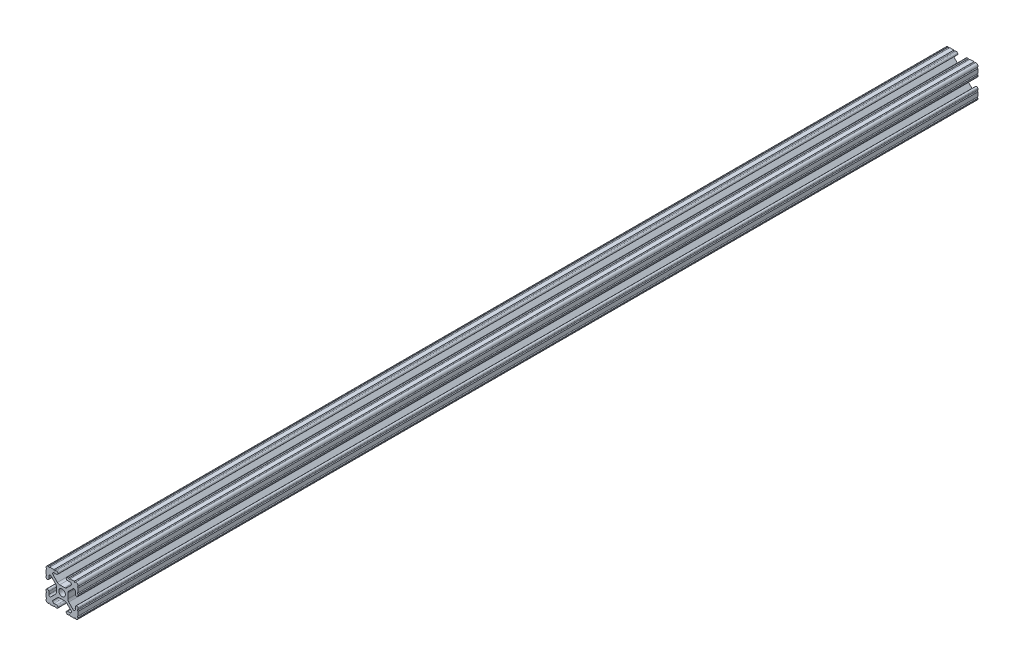
SolidWorks part; units mm, degrees
ref_plane "Front Plane" through (0, 0, 0) normal (0, 0, 1) x (1, 0, 0)
ref_plane "Top Plane" through (0, 0, 0) normal (0, 1, 0) x (1, 0, 0)
ref_plane "Right Plane" through (0, 0, 0) normal (1, 0, 0) x (0, 0, -1)
sketch "Sketch1" plane through (0, 0, 0) normal (0, 0, 1) x (1, 0, 0)
  line L0 (0, -12.7) -> (0, 12.7) construction
  line L1 (12.7, 0) -> (-12.7, 0) construction
  line L2 (3.2512, 12.7) -> (-3.2512, 12.7) construction
  line L3 (0, -4.5212) -> (0, 4.5212) construction
  line L4 (-3.2512, 12.7) -> (-3.2512, 10.4902) construction
  line L5 (12.7, -7.4168) -> (12.7, 7.4168) construction
  line L6 (0, -2.6035) -> (0, 2.6035) construction
  point P4 (0, 0)
  point P8 (0, 0)
  point P11 (0, 12.7)
  point P14 (0, 0)
  point P18 (12.7, 0)
  point P21 (0, 0)
sketch "Sketch2" plane through (0, 0, 0) normal (1, 0, 0) x (0, 0, -1)
  line L0 (-355.6, 0) -> (355.6, 0) construction
  point P4 (0, 0)
  dimension "Length" = 711.2
sketch "Sketch3" plane through (0, 0, 0) normal (0, 0, 1) x (1, 0, 0)
  line L1 (12.7, -12.7) -> (-12.7, -12.7)
  line L2 (12.7, -12.7) -> (12.7, 12.7)
  line L3 (12.7, 12.7) -> (-12.7, 12.7)
  line L4 (-12.7, -12.7) -> (-12.7, 12.7)
  line L5 (12.7, -12.7) -> (-12.7, 12.7) construction
  line L6 (12.7, 12.7) -> (-12.7, -12.7) construction
  point P0 (0, 0)
extrude "Boss-Extrude1" add sketch "Sketch3" along normal up to vertex (355.6 mm away) and the other way up to vertex (355.6 mm away) up to point (0, 0, 355.6) other way up to point (0, 0, -355.6)
sketch "Sketch4" plane through (0, 0, 355.6) normal (0, 0, 1) x (1, 0, 0)
  line L0 (-3.2512, 12.7) -> (-3.2512, 10.4902)
  line L1 (-3.2512, 10.4902) -> (-8.9276, 10.4902)
  line L2 (-8.9276, 10.4902) -> (-2.9586, 4.5212)
  line L3 (-2.9586, 4.5212) -> (2.9586, 4.5212)
  line L4 (0, -12.7) -> (0, 12.7) construction
  line L5 (12.7, 12.7) -> (-12.7, 12.7) construction
  line L6 (0, 12.7) -> (0, -12.7) construction
  line L7 (-12.7, 0) -> (12.7, 0) construction
  line L8 (-12.7, 12.7) -> (0, 0) construction
  line L9 (-12.7, 3.2512) -> (-10.4902, 3.2512)
  line L10 (-10.4902, 3.2512) -> (-10.4902, 8.9276)
  line L11 (-10.4902, 8.9276) -> (-4.5212, 2.9586)
  line L12 (-4.5212, 2.9586) -> (-4.5212, -2.9586)
  line L13 (4.5212, 2.9586) -> (4.5212, -2.9586)
  line L14 (10.4902, 8.9276) -> (4.5212, 2.9586)
  line L15 (10.4902, 3.2512) -> (10.4902, 8.9276)
  line L16 (12.7, 3.2512) -> (10.4902, 3.2512)
  line L17 (8.9276, 10.4902) -> (2.9586, 4.5212)
  line L18 (3.2512, 10.4902) -> (8.9276, 10.4902)
  line L19 (3.2512, 12.7) -> (3.2512, 10.4902)
  line L20 (3.2512, -12.7) -> (3.2512, -10.4902)
  line L21 (3.2512, -10.4902) -> (8.9276, -10.4902)
  line L22 (8.9276, -10.4902) -> (2.9586, -4.5212)
  line L23 (12.7, -3.2512) -> (10.4902, -3.2512)
  line L24 (10.4902, -3.2512) -> (10.4902, -8.9276)
  line L25 (10.4902, -8.9276) -> (4.5212, -2.9586)
  line L26 (-10.4902, -8.9276) -> (-4.5212, -2.9586)
  line L27 (-10.4902, -3.2512) -> (-10.4902, -8.9276)
  line L28 (-12.7, -3.2512) -> (-10.4902, -3.2512)
  line L29 (-2.9586, -4.5212) -> (2.9586, -4.5212)
  line L30 (-8.9276, -10.4902) -> (-2.9586, -4.5212)
  line L31 (-3.2512, -10.4902) -> (-8.9276, -10.4902)
  line L32 (-3.2512, -12.7) -> (-3.2512, -10.4902)
  line L33 (-12.7, 3.2512) -> (-12.7, -3.2512)
  line L34 (-3.2512, -12.7) -> (3.2512, -12.7)
  line L35 (12.7, -3.2512) -> (12.7, 3.2512)
  line L36 (3.2512, 12.7) -> (-3.2512, 12.7)
  line L37 (-12.7, 12.7) -> (-12.7, -12.7) construction
  line L38 (-12.7, -12.7) -> (12.7, -12.7) construction
  arc A3 (-6.3485, 10.4902) -> (-7.1039, 8.6665) centre (-6.3485, 9.4219) ccw
  arc A4 (7.1039, 8.6665) -> (6.3485, 10.4902) centre (6.3485, 9.4219) ccw
  arc A5 (8.6665, -7.1039) -> (10.4902, -6.3485) centre (9.4219, -6.3485) ccw
  arc A6 (10.4902, 6.3485) -> (8.6665, 7.1039) centre (9.4219, 6.3485) ccw
  arc A7 (-7.1039, -8.6665) -> (-6.3485, -10.4902) centre (-6.3485, -9.4219) ccw
  arc A8 (6.3485, -10.4902) -> (7.1039, -8.6665) centre (6.3485, -9.4219) ccw
  arc A9 (-8.6665, 7.1039) -> (-10.4902, 6.3485) centre (-9.4219, 6.3485) ccw
  arc A10 (-10.4902, -6.3485) -> (-8.6665, -7.1039) centre (-9.4219, -6.3485) ccw
  circle A11 centre (0, 0) radius 2.6035
  point P34 (0, 4.5212)
  point P45 (4.5212, 0)
  point P46 (-4.5212, 0)
  point P53 (0, -4.5212)
  point P81 (0, 0)
  line M2 (-12.7, 12.7) -> (-12.7, -12.7)
  line M3 (-12.7, -12.7) -> (12.7, -12.7)
  line M4 (12.7, -12.7) -> (12.7, 12.7)
  line M5 (12.7, 12.7) -> (-12.7, 12.7)
  dimension "D5" = 5.207
  dimension "D1" = 2.2098
  dimension "D2" = 2.2098
  dimension "D3" = 14.8336
  dimension "D4" = 4
extrude "Cut-Extrude1" cut sketch "Sketch4" against normal through all contours L17 A4 L18 L19 L0 L1 A3 L2 L3 M5 | L15 A6 L14 L13 L25 A5 L24 L23 L16 M4 | L21 A8 L22 L29 L30 A7 L31 L32 L20 M3 | L27 A10 L26 L12 L11 A9 L10 L9 L28 M2 | A11
sketch "Sketch5" plane through (0, 0, 355.6) normal (0, 0, 1) x (1, 0, 0)
  line L0 (-4.3561, 12.7) -> (-3.2512, 12.7)
  line L1 (-3.2512, 12.7) -> (-3.2512, 10.4902)
  line L2 (-3.2512, 10.4902) -> (-4.3561, 10.4902)
  line L3 (0, -12.7) -> (0, 12.7) construction
  line L4 (-3.2512, 12.7) -> (-12.7, 12.7) construction
  line L5 (3.2512, 10.4902) -> (4.3561, 10.4902)
  line L6 (3.2512, 12.7) -> (3.2512, 10.4902)
  line L7 (4.3561, 12.7) -> (3.2512, 12.7)
  line L8 (12.7, 4.3561) -> (12.7, 3.2512)
  line L9 (12.7, 3.2512) -> (10.4902, 3.2512)
  line L10 (10.4902, 3.2512) -> (10.4902, 4.3561)
  line L11 (10.4902, -3.2512) -> (10.4902, -4.3561)
  line L12 (12.7, -3.2512) -> (10.4902, -3.2512)
  line L13 (12.7, -4.3561) -> (12.7, -3.2512)
  line L14 (4.3561, -12.7) -> (3.2512, -12.7)
  line L15 (3.2512, -12.7) -> (3.2512, -10.4902)
  line L16 (3.2512, -10.4902) -> (4.3561, -10.4902)
  line L17 (-3.2512, -10.4902) -> (-4.3561, -10.4902)
  line L18 (-3.2512, -12.7) -> (-3.2512, -10.4902)
  line L19 (-4.3561, -12.7) -> (-3.2512, -12.7)
  line L20 (-12.7, -4.3561) -> (-12.7, -3.2512)
  line L21 (-12.7, -3.2512) -> (-10.4902, -3.2512)
  line L22 (-10.4902, -3.2512) -> (-10.4902, -4.3561)
  line L23 (-10.4902, 3.2512) -> (-10.4902, 4.3561)
  line L24 (-12.7, 3.2512) -> (-10.4902, 3.2512)
  line L25 (-12.7, 4.3561) -> (-12.7, 3.2512)
  line L26 (-12.7, 12.7) -> (-12.7, 3.2512) construction
  line L27 (-10.7124, 12.7) -> (-9.6075, 12.7)
  line L28 (-6.3436, 12.7) -> (-5.2387, 12.7)
  line L29 (-12.7, 10.7124) -> (-12.7, 9.6075)
  line L30 (-12.7, 6.3436) -> (-12.7, 5.2387)
  line L31 (6.3437, 12.7) -> (5.2388, 12.7)
  line L32 (10.7125, 12.7) -> (9.6076, 12.7)
  line L33 (12.7, 10.7125) -> (12.7, 9.6075)
  line L34 (12.7, 6.3436) -> (12.7, 5.2387)
  line L35 (12.7, -6.3437) -> (12.7, -5.2388)
  line L36 (12.7, -10.7125) -> (12.7, -9.6076)
  line L37 (10.7125, -12.7) -> (9.6076, -12.7)
  line L38 (6.3437, -12.7) -> (5.2388, -12.7)
  line L39 (-6.3436, -12.7) -> (-5.2387, -12.7)
  line L40 (-10.7124, -12.7) -> (-9.6075, -12.7)
  line L41 (-12.7, -10.7125) -> (-12.7, -9.6076)
  line L42 (-12.7, -6.3437) -> (-12.7, -5.2388)
  line L43 (12.7, 12.7) -> (3.2512, 12.7) construction
  line L44 (12.7, 3.2512) -> (12.7, 12.7) construction
  arc A0 (-4.3561, 10.4902) -> (-4.3561, 12.7) centre (-4.3561, 11.5951) ccw
  arc A1 (4.3561, 10.4902) -> (4.3561, 12.7) centre (4.3561, 11.5951) cw
  arc A2 (10.4902, 4.3561) -> (12.7, 4.3561) centre (11.5951, 4.3561) ccw
  arc A3 (10.4902, -4.3561) -> (12.7, -4.3561) centre (11.5951, -4.3561) cw
  arc A4 (4.3561, -10.4902) -> (4.3561, -12.7) centre (4.3561, -11.5951) ccw
  arc A5 (-4.3561, -10.4902) -> (-4.3561, -12.7) centre (-4.3561, -11.5951) cw
  arc A6 (-10.4902, -4.3561) -> (-12.7, -4.3561) centre (-11.5951, -4.3561) ccw
  arc A7 (-10.4902, 4.3561) -> (-12.7, 4.3561) centre (-11.5951, 4.3561) cw
  arc A8 (-10.7124, 12.7) -> (-9.6075, 12.7) centre (-10.16, 12.7) ccw
  arc A9 (-6.3436, 12.7) -> (-5.2387, 12.7) centre (-5.7912, 12.7) ccw
  arc A10 (-12.7, 9.6075) -> (-12.7, 10.7124) centre (-12.7, 10.16) ccw
  arc A11 (-12.7, 5.2387) -> (-12.7, 6.3436) centre (-12.7, 5.7912) ccw
  arc A12 (5.2388, 12.7) -> (6.3437, 12.7) centre (5.7912, 12.7) ccw
  arc A13 (9.6076, 12.7) -> (10.7125, 12.7) centre (10.16, 12.7) ccw
  arc A14 (12.7, 10.7125) -> (12.7, 9.6075) centre (12.7, 10.16) ccw
  arc A15 (12.7, 6.3436) -> (12.7, 5.2387) centre (12.7, 5.7912) ccw
  arc A16 (12.7, -5.2388) -> (12.7, -6.3437) centre (12.7, -5.7912) ccw
  arc A17 (12.7, -9.6076) -> (12.7, -10.7125) centre (12.7, -10.16) ccw
  arc A18 (10.7125, -12.7) -> (9.6076, -12.7) centre (10.16, -12.7) ccw
  arc A19 (6.3437, -12.7) -> (5.2388, -12.7) centre (5.7912, -12.7) ccw
  arc A20 (-5.2387, -12.7) -> (-6.3436, -12.7) centre (-5.7912, -12.7) ccw
  arc A21 (-9.6075, -12.7) -> (-10.7124, -12.7) centre (-10.16, -12.7) ccw
  arc A22 (-12.7, -10.7125) -> (-12.7, -9.6076) centre (-12.7, -10.16) ccw
  arc A23 (-12.7, -6.3437) -> (-12.7, -5.2388) centre (-12.7, -5.7912) ccw
  point P11 (0, 0)
  point P52 (0, 0)
  point P104 (0, 0)
  line M5 (3.2512, -10.4902) -> (3.2512, -12.7)
  line M6 (3.2512, -12.7) -> (12.7, -12.7)
  line M7 (12.7, -12.7) -> (12.7, -3.2512)
  line M8 (12.7, -3.2512) -> (10.4902, -3.2512)
  line M9 (10.4902, -3.2512) -> (10.4902, -6.3485)
  line M15 (10.4902, 6.3485) -> (10.4902, 3.2512)
  line M16 (10.4902, 3.2512) -> (12.7, 3.2512)
  line M17 (12.7, 3.2512) -> (12.7, 12.7)
  line M18 (12.7, 12.7) -> (3.2512, 12.7)
  line M19 (3.2512, 12.7) -> (3.2512, 10.4902)
  line M20 (3.2512, 10.4902) -> (6.3485, 10.4902)
  line M26 (-6.3485, 10.4902) -> (-3.2512, 10.4902)
  line M27 (-3.2512, 10.4902) -> (-3.2512, 12.7)
  line M28 (-3.2512, 12.7) -> (-12.7, 12.7)
  line M29 (-12.7, 12.7) -> (-12.7, 3.2512)
  line M30 (-12.7, 3.2512) -> (-10.4902, 3.2512)
  line M31 (-10.4902, 3.2512) -> (-10.4902, 6.3485)
  line M37 (-10.4902, -6.3485) -> (-10.4902, -3.2512)
  line M38 (-10.4902, -3.2512) -> (-12.7, -3.2512)
  line M39 (-12.7, -3.2512) -> (-12.7, -12.7)
  line M40 (-12.7, -12.7) -> (-3.2512, -12.7)
  line M41 (-3.2512, -12.7) -> (-3.2512, -10.4902)
  line M42 (-3.2512, -10.4902) -> (-6.3485, -10.4902)
  line M48 (6.3485, -10.4902) -> (3.2512, -10.4902)
  dimension "D2" = 0.5524
  dimension "D3" = 2.54
  dimension "D4" = 2.54
  dimension "D5" = 2.54
  dimension "D6" = 2.54
  dimension "D1" = 4
  dimension "D7" = 4
extrude "Cut-Extrude2" cut sketch "Sketch5" against normal through all contours A7 M30 M29 | A7 L24 M31 | A6 L21 M39 | A6 M37 M38 | A5 L18 M42 | A5 M41 M40 | A4 M48 M5 | A4 L15 M6 | A3 L12 M9 | A3 M8 M7 | A2 M15 M16 | A2 L9 M17 | A1 M19 M18 | A1 L6 M20 | A0 L1 M28 | A0 M26 M27 | A11 L30 | A10 L29 | A8 L27 | A9 L28 | L31 A12 | L32 A13 | L33 A14 | L34 A15 | L42 A23 | L41 A22 | L40 A21 | L39 A20 | L36 A17 | L35 A16 | L37 A18 | L38 A19
fillet "Fillet1" radius 2.54 8 edges at (2.9586, -4.5212, 0) (-2.9586, -4.5212, 0) (4.5212, -2.9586, 0) (4.5212, 2.9586, 0) (-2.9586, 4.5212, 0) (2.9586, 4.5212, 0) (-4.5212, -2.9586, 0) (-4.5212, 2.9586, 0)
fillet "Fillet2" radius 1.778 4 edges at (12.7, -12.7, 0) (12.7, 12.7, 0) (-12.7, -12.7, 0) (-12.7, 12.7, 0)
equation "\"D2@Sketch4\"=\"Thickness@Sketch1\""
equation "\"D1@Sketch4\"=\"Thickness@Sketch1\""
equation "\"D3@Sketch4\"=\"Opening Width@Sketch1\""
equation "\"D5@Sketch4\"=\"Hole Dia@Sketch1\""
equation "\"D2@Sketch5\"=\"Thickness@Sketch1\"/4"
equation "\"D3@Sketch5\"=\"Height@Sketch1\"/10"
equation "\"D4@Sketch5\"=\"D3@Sketch5\""
equation "\"D5@Sketch5\"=\"D4@Sketch5\""
equation "\"D6@Sketch5\"=\"D5@Sketch5\""
